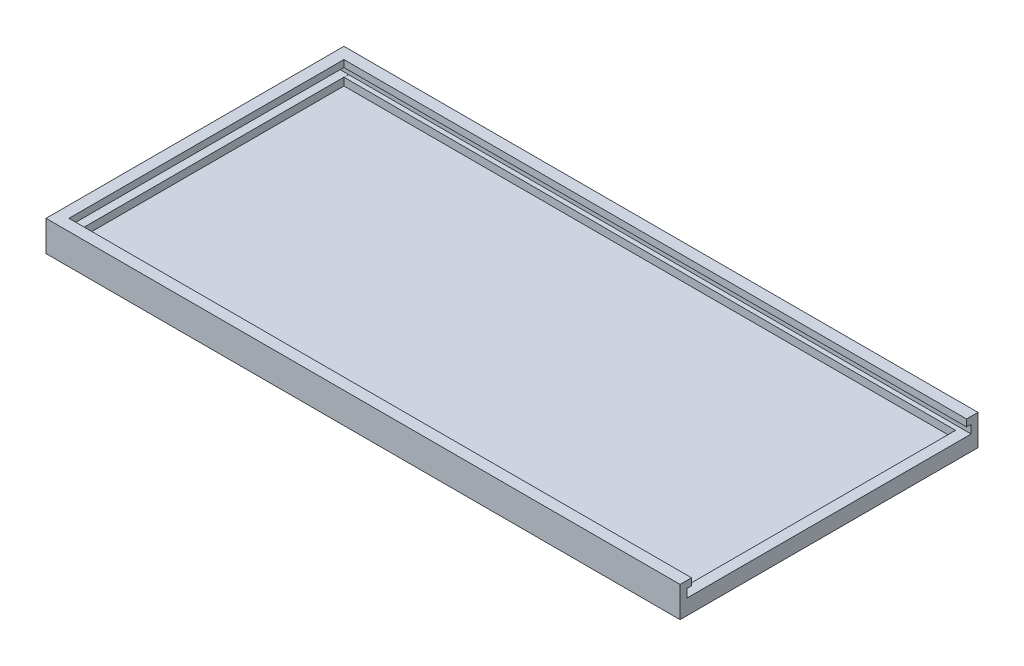
SolidWorks part; units mm, degrees
ref_plane "Спереди" through (0, 0, 0) normal (0, 0, 1) x (1, 0, 0)
ref_plane "Сверху" through (0, 0, 0) normal (0, 1, 0) x (1, 0, 0)
ref_plane "Справа" through (0, 0, 0) normal (1, 0, 0) x (0, 0, -1)
other "Configuration Table"
sketch "Эскиз1" plane through (0, 0, 0) normal (0, 1, 0) x (1, 0, 0)
  line L1 (0, 0) -> (166, 0)
  line L2 (0, 0) -> (0, 78)
  line L3 (0, 78) -> (166, 78)
  line L4 (166, 0) -> (166, 78)
  dimension "D1" = 166
  dimension "D2" = 78
extrude "Основание" add sketch "Эскиз1" along normal blind 8
sketch "Эскиз2" plane through (0, 8, 0) normal (0, 1, 0) x (1, 0, 0)
  line L0 (0, 78) -> (0, 0) construction
  line L1 (3, 75) -> (166, 75)
  line L2 (3, 75) -> (3, 3)
  line L3 (3, 3) -> (166, 3)
  line L4 (166, 75) -> (166, 3)
  line L5 (166, 78) -> (0, 78) construction
  line L6 (0, 0) -> (166, 0) construction
  dimension "D1" = 163
  dimension "D2" = 3
  dimension "D3" = 3
  dimension "D4" = 3
extrude "вырез в основе" cut sketch "Эскиз2" against normal blind 6
sketch "Эскиз7" plane through (0, 0, -75) normal (0, 0, 1) x (1, 0, 0)
  line L0 (166, 8) -> (166, 0) construction
  line L1 (3, 6.2) -> (166, 6.2)
  line L2 (3, 6.2) -> (3, 4)
  line L3 (3, 4) -> (166, 4)
  line L4 (166, 6.2) -> (166, 4)
  line L5 (0, 8) -> (0, 0) construction
  line L6 (0, 8) -> (166, 8) construction
  dimension "D1" = 3
  dimension "D2" = 2.2
  dimension "D3" = 1.8
extrude "Вырез-Вытянуть3" cut sketch "Эскиз7" against normal blind 1.2
sketch "Эскиз8" plane through (3, 0, 0) normal (1, 0, 0) x (0, 0, -1)
  line L0 (76.2, 6.2) -> (75, 6.2) construction
  line L1 (76.2, 6.2) -> (0.8, 6.2)
  line L2 (76.2, 6.2) -> (76.2, 4.0107)
  line L3 (76.2, 4.0107) -> (0.8, 4.0107)
  line L4 (0.8, 6.2) -> (0.8, 4.0107)
  line L5 (76.2, 6.2) -> (75, 6.2) construction
  line L6 (3, 2) -> (3, 8) construction
  line L7 (76.2, 6.2) -> (76.2, 4) construction
  dimension "D1" = 2.2
  dimension "D2" = 0
extrude "Вырез-Вытянуть4" cut sketch "Эскиз8" against normal blind 2.2
sketch "Эскиз9" plane through (0, 0, -3) normal (0, 0, -1) x (-1, 0, 0)
  line L0 (-3, 6.2) -> (-3, 4.0107) construction
  line L1 (-3, 6.2) -> (-166, 6.2)
  line L2 (-3, 6.2) -> (-3, 4)
  line L3 (-3, 4) -> (-166, 4)
  line L4 (-166, 6.2) -> (-166, 4)
  line L5 (-166, 8) -> (0, 8) construction
  dimension "D1" = 163
  dimension "D2" = 2.2
  dimension "D3" = 1.8
extrude "Вырез-Вытянуть5" cut sketch "Эскиз9" against normal blind 1.2
sketch "Эскиз10" plane through (0, 2, 0) normal (0, 1, 0) x (1, 0, 0)
  line L0 (166, 75) -> (3, 75) construction
  line L1 (163.1309, 75) -> (166, 75)
  line L2 (163.1309, 75) -> (163.1309, 3)
  line L3 (163.1309, 3) -> (166, 3)
  line L4 (166, 75) -> (166, 3)
  line L5 (3, 3) -> (166, 3) construction
  line L6 (166, 3) -> (166, 75) construction
extrude "Бобышка-Вытянуть1" add sketch "Эскиз10" along normal blind 2
